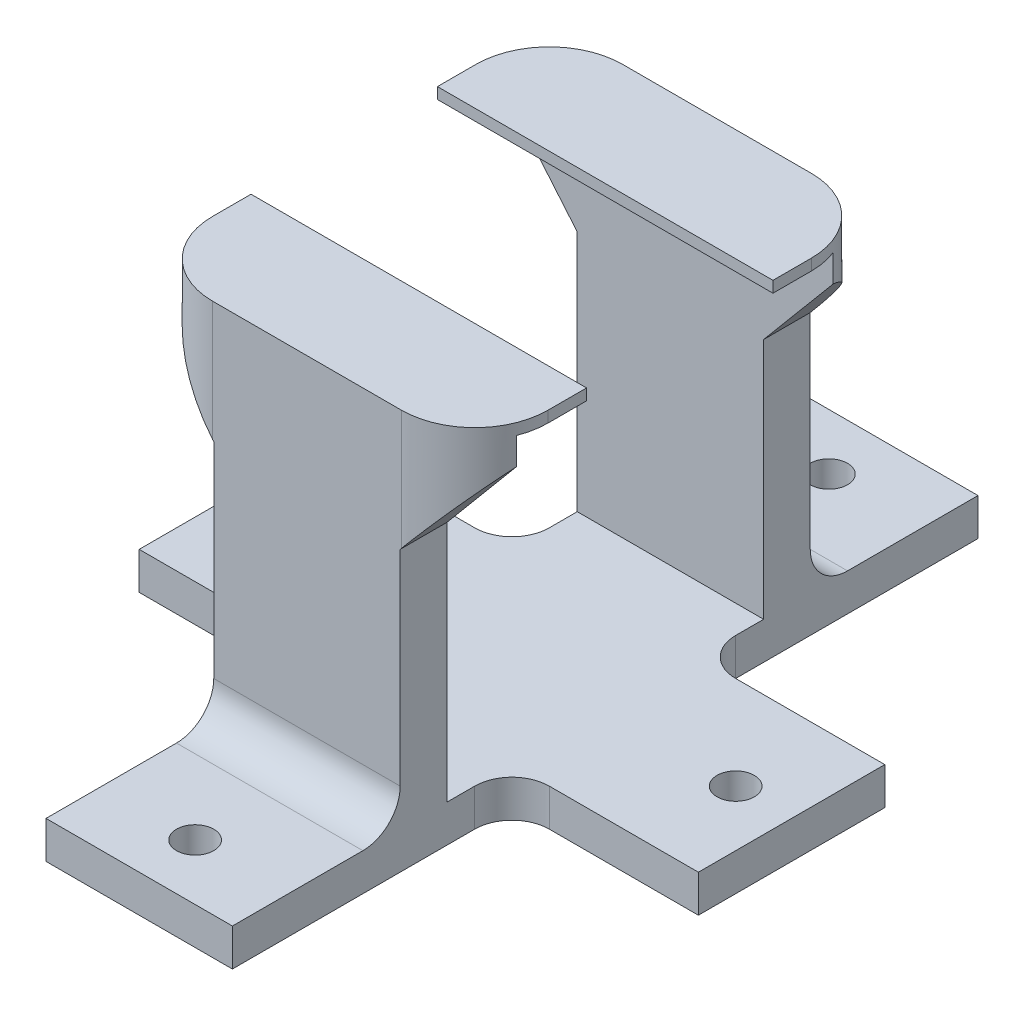
SolidWorks part; units mm, degrees
ref_plane "Front Plane" through (0, 0, 0) normal (0, 0, 1) x (1, 0, 0)
ref_plane "Top Plane" through (0, 0, 0) normal (0, 1, 0) x (1, 0, 0)
ref_plane "Right Plane" through (0, 0, 0) normal (1, 0, 0) x (0, 0, -1)
sketch "Sketch1" plane through (0, 0, 0) normal (1, 0, 0) x (0, 0, -1)
  line L0 (0, 0) -> (0, 5.08)
  line L3 (22.86, 5.08) -> (22.86, 52.07)
  line L4 (22.86, 52.07) -> (29.21, 52.07)
  line L5 (29.21, 52.07) -> (29.21, 5.08)
  line L7 (72.39, 5.08) -> (72.39, 52.07)
  line L8 (72.39, 52.07) -> (78.74, 52.07)
  line L9 (78.74, 52.07) -> (78.74, 5.08)
  line L12 (101.6, 5.08) -> (101.6, 0)
  line L13 (101.6, 0) -> (0, 0)
  line L14 (0, 5.08) -> (22.86, 5.08)
  line L20 (29.21, 5.08) -> (72.39, 5.08)
  line L25 (101.6, 5.08) -> (78.74, 5.08)
  point P3 (50.8, 0)
  point P23 (50.8, 5.08)
  dimension "D4" = 5.08
  dimension "D5" = 46.99
  dimension "D2" = 101.6
  dimension "D10" = 43.18
  dimension "D11" = 6.35
extrude "Base" add sketch "Sketch1" along normal blind 25.4
sketch "Sketch5" plane through (0, 0, -78.74) normal (0, 0, -1) x (-1, 0, 0)
  line L1 (-35.56, 52.07) -> (-35.56, 50.2082)
  line L2 (-25.4, 5.08) -> (-25.4, 52.07) construction
  line L5 (-35.56, 52.07) -> (-35.56, 54.61)
  line L6 (-35.56, 54.61) -> (10.16, 54.61)
  line L7 (-12.7, 54.61) -> (-12.7, 52.07) construction
  line L8 (-25.4, 52.07) -> (0, 52.07) construction
  line L10 (-25.4, 52.07) -> (0, 52.07)
  line L11 (-25.4, 38.1) -> (-25.4, 52.07)
  line L12 (-25.4, 52.07) -> (0, 52.07) construction
  line L13 (-35.56, 50.2082) -> (-25.4, 38.1)
  line L14 (10.16, 50.2082) -> (0, 38.1)
  line L15 (0, 38.1) -> (0, 52.07)
  line L16 (10.16, 52.07) -> (10.16, 54.61)
  line L17 (10.16, 52.07) -> (10.16, 50.2082)
  point P15 (-12.7, 52.07)
  dimension "D1" = 40
  dimension "D4" = 13.97
  dimension "D2" = 2.54
  dimension "D3" = 10.16
extrude "Boss-Extrude1" add sketch "Sketch5" against normal up to surface (6.35 mm away) up to face at (12.7, 28.575, -72.39)
ref_plane "Plane3" through (0, 0, -50.8) normal (0, 0, 1) x (1, 0, 0)
sketch "Sketch6" plane through (0, 0, -22.86) normal (0, 0, 1) x (1, 0, 0)
  line L0 (0, 52.07) -> (0, 5.08) construction
  line L1 (25.4, 52.07) -> (0, 52.07) construction
  line L2 (25.4, 52.07) -> (25.4, 5.08) construction
  line L3 (25.4, 38.1) -> (35.56, 50.2082) construction
  line L4 (35.56, 50.2082) -> (35.56, 54.61) construction
  line L5 (35.56, 54.61) -> (-10.16, 54.61) construction
  line L6 (-10.16, 54.61) -> (-10.16, 50.2082) construction
  line L7 (-10.16, 50.2082) -> (0, 38.1) construction
  line L8 (0, 52.07) -> (0, 38.1)
  line L9 (25.4, 52.07) -> (0, 52.07)
  line L10 (25.4, 52.07) -> (25.4, 38.1)
  line L11 (25.4, 38.1) -> (35.56, 50.2082)
  line L12 (35.56, 50.2082) -> (35.56, 54.61)
  line L13 (35.56, 54.61) -> (-10.16, 54.61)
  line L14 (-10.16, 54.61) -> (-10.16, 50.2082)
  line L15 (-10.16, 50.2082) -> (0, 38.1)
extrude "Boss-Extrude2" add sketch "Sketch6" against normal up to surface (6.35 mm away) up to face at (12.7, 28.575, -29.21)
sketch "Sketch7" plane through (0, 0, -72.39) normal (0, 0, 1) x (1, 0, 0)
  line L0 (35.56, 50.2082) -> (35.56, 54.61) construction
  line L1 (-10.16, 54.61) -> (35.56, 54.61)
  line L2 (-10.16, 54.61) -> (-10.16, 53.086)
  line L3 (-10.16, 53.086) -> (35.56, 53.086)
  line L4 (35.56, 54.61) -> (35.56, 53.086)
  dimension "D1" = 1.524
extrude "Boss-Extrude3" add sketch "Sketch7" along normal blind 8.89
mirror "Mirror19" about plane through (0, 0, -50.8) normal (0, 0, 1) of "Boss-Extrude3"
sketch "Sketch3" plane through (25.4, 0, 0) normal (1, 0, 0) x (0, 0, -1)
  line L0 (0, 0) -> (101.6, 0) construction
  line L1 (63.5, 0) -> (38.1, 0)
  line L5 (0, 0) -> (101.6, 0) construction
  line L6 (63.5, 0) -> (63.5, 5.08)
  line L9 (72.39, 5.08) -> (29.21, 5.08) construction
  line L10 (63.5, 5.08) -> (38.1, 5.08)
  line L11 (38.1, 5.08) -> (38.1, 0)
  point P1 (50.8, 0)
  point P9 (50.8, 0)
  dimension "D1" = 25.4
extrude "Front Screw Support" add sketch "Sketch3" along normal blind 25.4
ref_plane "Plane1" through (12.7, 0, 0) normal (1, 0, 0) x (0, 0, -1)
mirror "Mirror3" about plane through (12.7, 0, 0) normal (1, 0, 0) of "Front Screw Support"
fillet "Front Screw Support Fillet" [suppressed] radius 10.16
sketch "Sketch4" plane through (0, 5.08, 0) normal (0, 1, 0) x (1, 0, 0)
  line L0 (-25.4, 50.8) -> (50.8, 50.8) construction
  line L3 (50.8, 63.5) -> (50.8, 38.1) construction
  line L4 (-25.4, 63.5) -> (-25.4, 38.1) construction
  line L5 (50.8, 63.5) -> (50.8, 38.1) construction
  line L6 (12.7, 7.62) -> (12.7, 93.98) construction
  line L7 (25.4, 101.6) -> (0, 101.6) construction
  circle A0 centre (-17.78, 50.8) radius 2.54
  circle A1 centre (43.18, 50.8) radius 2.54
  circle A2 centre (12.7, 93.98) radius 2.54
  circle A3 centre (12.7, 7.62) radius 2.54
  point P11 (12.7, 50.8)
  point P15 (50.8, 50.8)
  dimension "D3" = 5.08
  dimension "D1" = 7.62
  dimension "D2" = 7.62
  dimension "D4" = 7.62
extrude "Cut-Extrude1" cut sketch "Sketch4" along direction (0, 1, 0) on the side against the normal up to next (5.08 mm away)
fillet "Fillet2" [suppressed] radius 5.08
fillet "Fillet3" radius 10 4 edges at (35.56, 52.4091, -78.74) (-10.16, 52.4091, -78.74) (-10.16, 52.4091, -22.86) (35.56, 52.4091, -22.86)
fillet "Fillet4" radius 5.08 6 edges at (25.4, 2.54, -63.5) (25.4, 2.54, -38.1) (0, 2.54, -38.1) (0, 2.54, -63.5) (12.7, 5.08, -78.74) (12.7, 5.08, -22.86)
